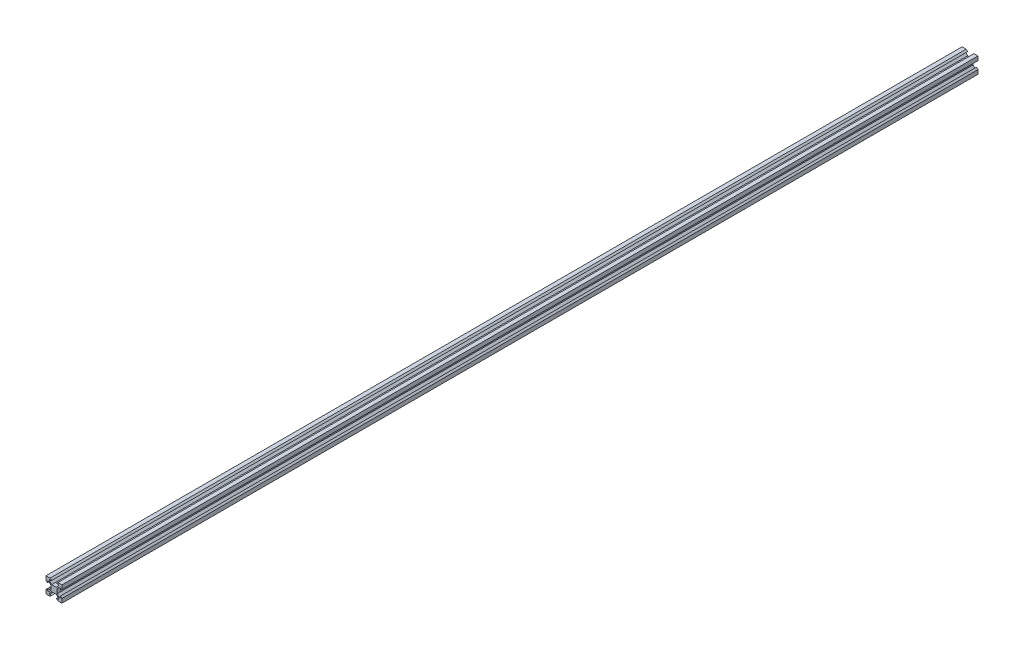
SolidWorks part; units mm, degrees
ref_plane "Front Plane" through (0, 0, 0) normal (0, 0, 1) x (1, 0, 0)
ref_plane "Top Plane" through (0, 0, 0) normal (0, 1, 0) x (1, 0, 0)
ref_plane "Right Plane" through (0, 0, 0) normal (1, 0, 0) x (0, 0, -1)
sketch "Sketch1" plane through (0, 0, 0) normal (0, 0, 1) x (1, 0, 0)
  line L1 (0, 0) -> (20, 0)
  line L2 (0, 0) -> (0, 20)
  line L3 (0, 20) -> (20, 20)
  line L4 (20, 0) -> (20, 20)
  line L5 (0, 0) -> (20, 20) construction
  line L6 (0, 20) -> (20, 0) construction
  point P4 (10, 10)
  dimension "D1" = 20
  dimension "D2" = 20
extrude "Boss-Extrude1" add sketch "Sketch1" along normal blind 1153.3
sketch "Sketch2" plane through (0, 0, 1153.3) normal (0, 0, 1) x (1, 0, 0)
  line L4 (0, 0) -> (20, 20) construction
  line L5 (4.5, 18.18) -> (6.94, 18.18)
  line L6 (4.5, 16.4758) -> (4.5, 18.18)
  line L15 (7.1658, 13.81) -> (4.5, 16.4758)
  line L17 (12.8342, 13.81) -> (7.1658, 13.81)
  line L27 (15.5, 16.4758) -> (12.8342, 13.81)
  line L29 (15.5, 18.18) -> (15.5, 16.4758)
  line L31 (13.06, 18.18) -> (15.5, 18.18)
  line L33 (14.88, 20) -> (5.12, 20)
  line L35 (6.94, 18.18) -> (5.12, 20)
  line L54 (14.88, 20) -> (13.06, 18.18)
  line L56 (14.88, 0) -> (13.06, 1.82)
  line L57 (6.94, 1.82) -> (5.12, 0)
  line L58 (14.88, 0) -> (5.12, 0)
  line L68 (13.06, 1.82) -> (15.5, 1.82)
  line L71 (15.5, 1.82) -> (15.5, 3.5242)
  line L81 (15.5, 3.5242) -> (12.8342, 6.19)
  line L82 (12.8342, 6.19) -> (7.1658, 6.19)
  line L83 (7.1658, 6.19) -> (4.5, 3.5242)
  line L84 (4.5, 3.5242) -> (4.5, 1.82)
  line L85 (4.5, 1.82) -> (6.94, 1.82)
  line L136 (20, 0) -> (10, 0) construction
  line L137 (0, 0) -> (20, 0) construction
  line L186 (1.82, 4.5) -> (1.82, 6.94)
  line L187 (3.5242, 4.5) -> (1.82, 4.5)
  line L188 (6.19, 7.1658) -> (3.5242, 4.5)
  line L189 (6.19, 12.8342) -> (6.19, 7.1658)
  line L190 (3.5242, 15.5) -> (6.19, 12.8342)
  line L191 (1.82, 15.5) -> (3.5242, 15.5)
  line L192 (1.82, 13.06) -> (1.82, 15.5)
  line L193 (0, 14.88) -> (0, 5.12)
  line L194 (1.82, 6.94) -> (0, 5.12)
  line L195 (0, 14.88) -> (1.82, 13.06)
  line L203 (20, 14.88) -> (18.18, 13.06)
  line L205 (18.18, 6.94) -> (20, 5.12)
  line L206 (20, 14.88) -> (20, 5.12)
  line L207 (18.18, 13.06) -> (18.18, 15.5)
  line L208 (18.18, 15.5) -> (16.4758, 15.5)
  line L209 (16.4758, 15.5) -> (13.81, 12.8342)
  line L210 (13.81, 12.8342) -> (13.81, 7.1658)
  line L211 (13.81, 7.1658) -> (16.4758, 4.5)
  line L212 (16.4758, 4.5) -> (18.18, 4.5)
  line L213 (18.18, 4.5) -> (18.18, 6.94)
extrude "Cut-Extrude1" cut sketch "Sketch2" against normal through all
